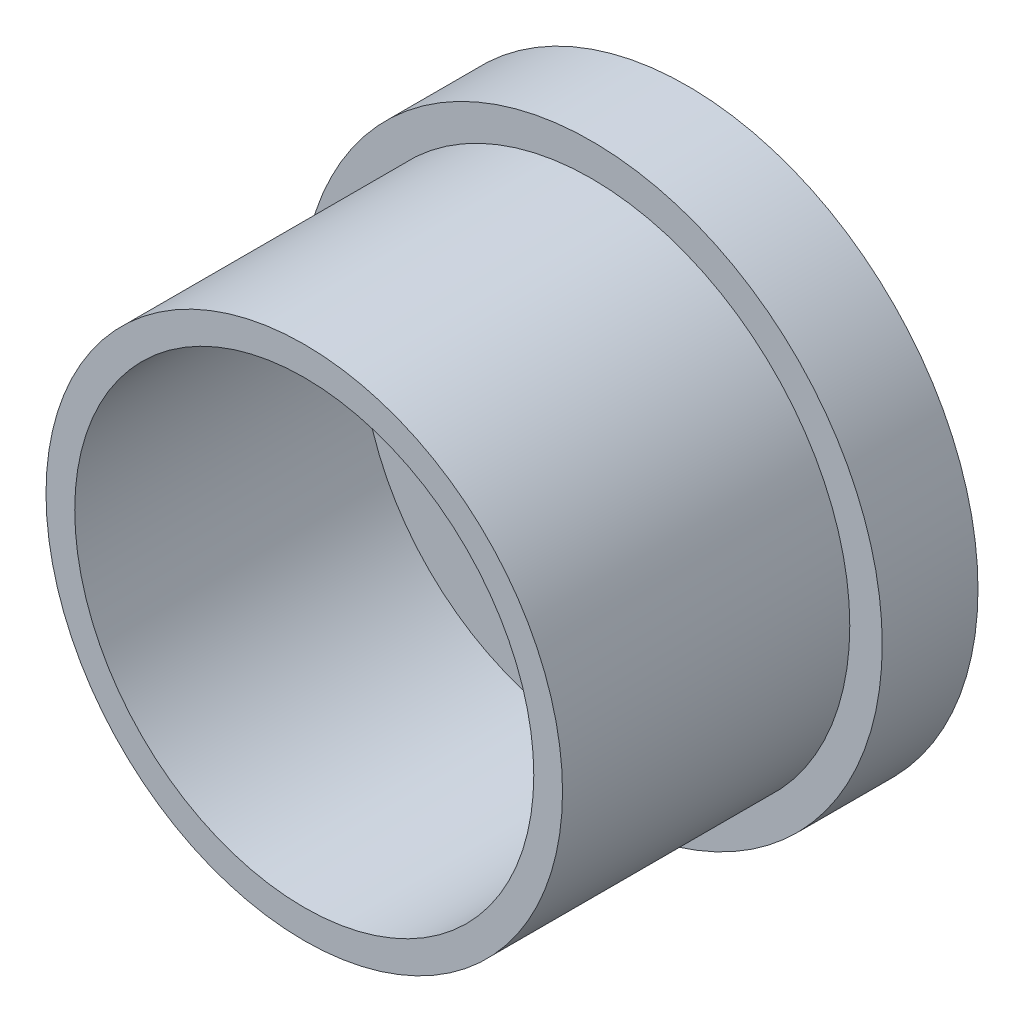
SolidWorks part; units mm, degrees
ref_plane "Front Plane" through (0, 0, 0) normal (0, 0, 1) x (1, 0, 0)
ref_plane "Top Plane" through (0, 0, 0) normal (0, 1, 0) x (1, 0, 0)
ref_plane "Right Plane" through (0, 0, 0) normal (1, 0, 0) x (0, 0, -1)
sketch "Sketch3" plane through (0, 0, 0) normal (0, 0, 1) x (1, 0, 0)
  line L0 (-35, 10.5) -> (-10.5, 10.5) construction
  line L1 (-35, 19.3197) -> (-10.5, 19.3197)
  line L2 (-35, 1.6803) -> (-10.5, 1.6803)
  line L3 (0, 21) -> (-45.5, 21) construction
  line L4 (-28.75, 0) -> (-16.75, 0)
  line L5 (-28.75, 0) -> (-28.75, 3)
  line L6 (-28.75, 3) -> (-16.75, 3)
  line L7 (-16.75, 0) -> (-16.75, 3)
  line L8 (-28.3781, 21) -> (-17.0742, 21)
  line L9 (-28.3781, 21) -> (-28.3781, 16.1322)
  line L10 (-28.3781, 16.1322) -> (-17.0742, 16.1322)
  line L11 (-17.0742, 21) -> (-17.0742, 16.1322)
  line L12 (-45.5, 21) -> (-45.5, 0) construction
  line L13 (0, 0) -> (0, 21) construction
  arc A0 (-35, 19.3197) -> (-35, 1.6803) centre (-35, 10.5) ccw
  arc A1 (-10.5, 1.6803) -> (-10.5, 19.3197) centre (-10.5, 10.5) ccw
  circle A2 centre (-22.75, 10.5) radius 30.3584
  circle A3 centre (-35, 10.5) radius 8 construction
  point P4 (-22.75, 10.5)
  dimension "D1" = 0.8197
  dimension "D2" = 17.1219
  dimension "D3" = 17.0742
  dimension "D4" = 4.8678
extrude "Boss-Extrude2" add sketch "Sketch3" along normal blind 10 contours A2 A1 L2 L7 L4 L5 A0 L1 L9 L8 L11
sketch "Sketch4" plane through (0, 0, 10) normal (0, 0, 1) x (1, 0, 0)
  circle A0 centre (-22.75, 10.5) radius 23.97
  circle A1 centre (-22.75, 10.5) radius 26.97
  dimension "D1" = 3
extrude "Boss-Extrude3" add sketch "Sketch4" along normal blind 30 contours A1 | A0
